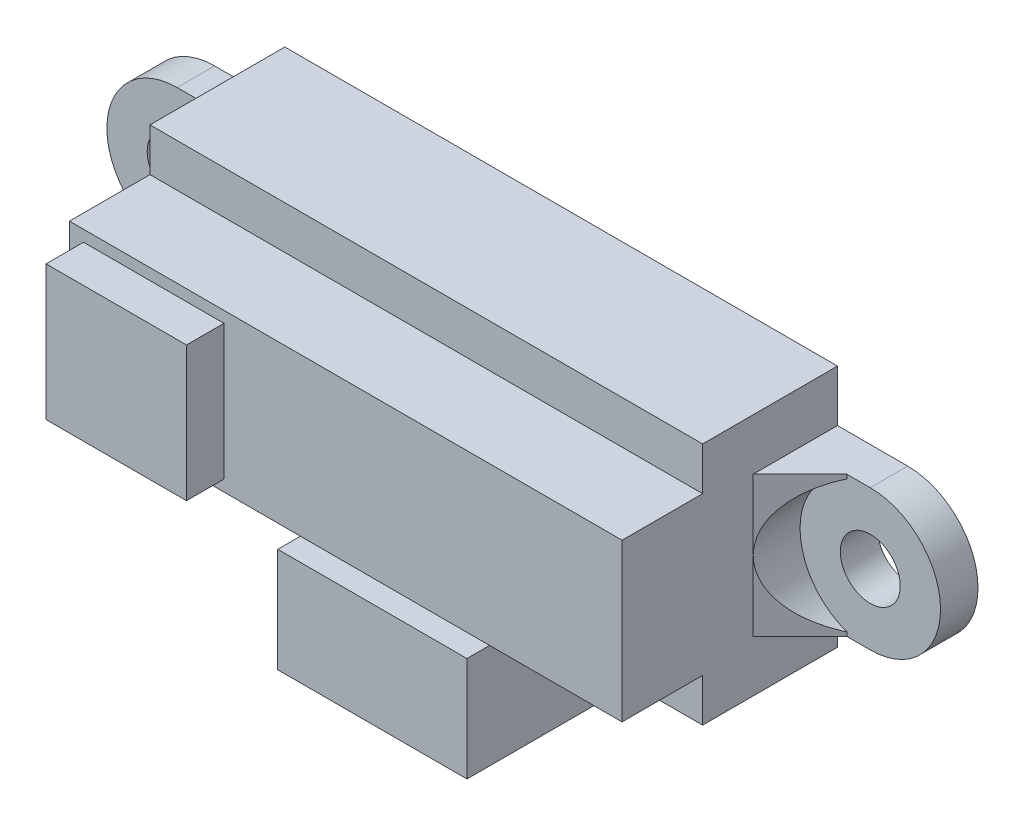
SolidWorks part; units mm, degrees
ref_plane "Plan de face" through (0, 0, 0) normal (0, 0, 1) x (1, 0, 0)
ref_plane "Plan de dessus" through (0, 0, 0) normal (0, 1, 0) x (1, 0, 0)
ref_plane "Plan de droite" through (0, 0, 0) normal (1, 0, 0) x (0, 0, -1)
ref_plane "Plan1" through (0, 0, 11.5) normal (0, 0, 1) x (1, 0, 0)
sketch "Esquisse1" plane through (0, 0, 11.5) normal (0, 0, 1) x (1, 0, 0)
  line L0 (-14.75, 6.5) -> (-14.75, -6.5)
  line L1 (-14.75, -6.5) -> (14.75, -6.5)
  line L2 (14.75, -6.5) -> (14.75, 6.5)
  line L3 (14.75, 6.5) -> (-14.75, 6.5)
extrude "Boss.-Extru.1" add sketch "Esquisse1" against normal blind 11.5
sketch "Esquisse2" plane through (14.75, 0, 0) normal (1, 0, 0) x (0, 0, -1)
  line L0 (-11.5, -6.5) -> (-7.2, -6.5)
  line L1 (-7.2, -6.5) -> (-7.2, -4.2)
  line L2 (-7.2, -4.2) -> (-11.5, -4.2)
  line L3 (-11.5, -4.2) -> (-11.5, -6.5)
extrude "Enlèv. mat.-Extru.1" cut sketch "Esquisse2" against normal through all
sketch "Esquisse3" plane through (14.75, 0, 0) normal (1, 0, 0) x (0, 0, -1)
  line L0 (-11.5, 4.2) -> (-7.2, 4.2)
  line L1 (-7.2, 4.2) -> (-7.2, 6.5)
  line L2 (-7.2, 6.5) -> (-11.5, 6.5)
  line L3 (-11.5, 6.5) -> (-11.5, 4.2)
extrude "Enlèv. mat.-Extru.2" cut sketch "Esquisse3" against normal through all
ref_plane "Plan2" through (0, 0, 0) normal (0, 0, -1) x (-1, 0, 0)
sketch "Esquisse4" plane through (0, 0, 0) normal (0, 0, -1) x (-1, 0, 0)
  line L0 (-14.75, -3.75) -> (-14.75, 3.75)
  line L1 (-14.75, 3.75) -> (-18.5, 3.75)
  line L2 (-18.5, -3.75) -> (-14.75, -3.75)
  arc A0 (-18.5, 3.75) -> (-18.5, -3.75) centre (-18.5, 0) ccw
extrude "Boss.-Extru.2" add sketch "Esquisse4" against normal blind 2
sketch "Esquisse5" plane through (0, 0, 0) normal (0, 0, -1) x (-1, 0, 0)
  line L0 (18.5, 3.75) -> (14.75, 3.75)
  line L1 (14.75, 3.75) -> (14.75, -3.75)
  line L2 (14.75, -3.75) -> (18.5, -3.75)
  arc A0 (18.5, -3.75) -> (18.5, 3.75) centre (18.5, 0) ccw
extrude "Boss.-Extru.3" add sketch "Esquisse5" against normal blind 2
sketch "Esquisse6" plane through (0, 0, 11.5) normal (0, 0, 1) x (1, 0, 0)
  line L0 (-14, 3.6) -> (-6.5, 3.6)
  line L1 (-6.5, 3.6) -> (-6.5, -3.6)
  line L2 (-6.5, -3.6) -> (-14, -3.6)
  line L3 (-14, -3.6) -> (-14, 3.6)
extrude "Boss.-Extru.4" add sketch "Esquisse6" along normal blind 2
hole_wizard "Diamètre du perçage Ø3.2 (3.2)1" positions "Esquisse8" profile "Esquisse7" hole size "Ø3.2" standard "Ansi Metric"
sketch "Esquisse8" plane through (0, 0, 0) normal (0, 0, -1) x (-1, 0, 0)
  point P0 (-18.5, 0)
  point P1 (18.5, 0)
sketch "Esquisse7" plane through (18.5, 0, 0) normal (1, 0, 0) x (0, 1, 0)
  line L0 (0, 0) -> (0, 13.5)
  line L1 (0, 13.5) -> (1.6, 13.5)
  line L2 (1.6, 13.5) -> (1.6, 0)
  line L5 (1.6, 0) -> (0, 0)
  line L11 (0, -6.35) -> (0, 107.95) construction
  dimension "Diamètre du perçage jusqu'au prochain" = 3.2
  dimension "Profondeur du perçage jusqu'au prochain" = 13.5
sketch "Esquisse9" plane through (0, 0, 0) normal (1, 0, 0) x (0, 0, -1)
  line L0 (-8.51, -6.83) -> (-10.08, -6.83)
  line L1 (-10.08, -6.83) -> (-10.08, -12.4)
  line L2 (-10.08, -12.4) -> (-3.3, -12.4)
  line L3 (-3.3, -12.4) -> (-3.3, -6.5)
  line L4 (-7.2, -5.9647) -> (-8.51, -6.83)
  line L5 (-3.3, -6.5) -> (-7.2, -6.5)
  line L6 (-7.2, -6.5) -> (-7.2, -5.9647)
  dimension "D1" = 5.57
  dimension "D2" = 6.78
  dimension "D3" = 5.9
  dimension "D4" = 3.9
  dimension "D5" = 1.57
  dimension "D6" = 1.57
  dimension "D7" = 0.5353
extrude "Boss.-Extru.5" add sketch "Esquisse9" along normal blind 5.05 and the other way blind 5.05
sketch "Esquisse10" plane through (0, 3.75, 0) normal (0, 1, 0) x (1, 0, 0)
  line L0 (14.75, -2) -> (14.75, -4.5)
  line L1 (14.75, 0) -> (14.75, -7.2) construction
  line L2 (14.75, -4.5) -> (17.25, -2)
  line L3 (14.75, -2) -> (18.5, -2) construction
  line L4 (17.25, -2) -> (14.75, -2)
  line L5 (-14.75, -2) -> (-14.75, -4.5)
  line L6 (-14.75, 0) -> (-14.75, -7.2) construction
  line L7 (-14.75, -4.5) -> (-17.25, -2)
  line L8 (-18.5, -2) -> (-14.75, -2) construction
  line L9 (-17.25, -2) -> (-14.75, -2)
  dimension "D1" = 2.5
  dimension "D2" = 2.5
  dimension "D3" = 2.5
  dimension "D4" = 2.5
extrude "Boss.-Extru.6" add sketch "Esquisse10" against normal up to surface (7.5 mm away) up to face at (-16.625, -3.75, 1)
sketch "Esquisse11" plane through (0, 0, 11.5) normal (0, 0, 1) x (1, 0, 0)
  circle A0 centre (18.5, 0) radius 3.75
  circle A1 centre (-18.5, 0) radius 3.75
  dimension "D1" = 18.5
  dimension "D2" = 18.5
extrude "Enlèv. mat.-Extru.3" cut sketch "Esquisse11" against normal up to surface (9.5 mm away) up to face at (-18.7667, 0, 2)
